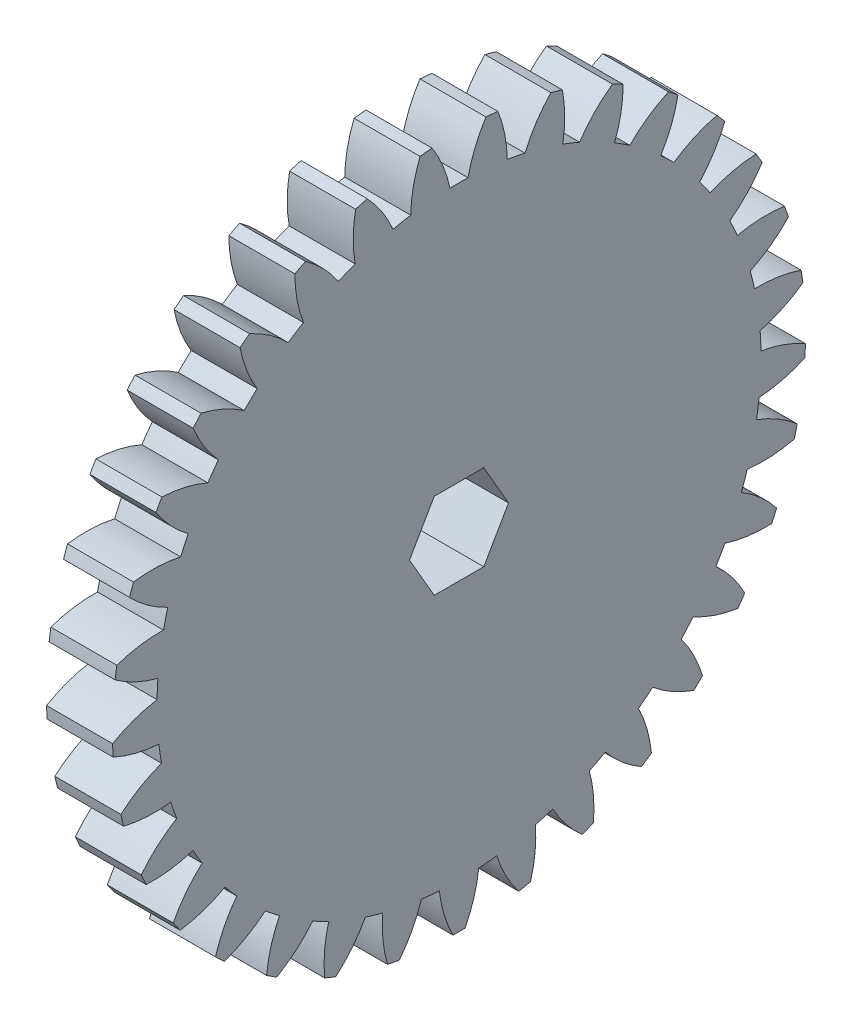
SolidWorks part; units mm, degrees
ref_plane "Plane1" through (0, 0, 0) normal (0, 0, 1) x (1, 0, 0)
ref_plane "Plane2" through (0, 0, 0) normal (0, 1, 0) x (1, 0, 0)
ref_plane "Plane3" through (0, 0, 0) normal (1, 0, 0) x (0, 0, -1)
sketch "HoldingSke" plane through (0, 0, 0) normal (0, 1, 0) x (1, 0, 0)
  line L0 (0, 0) -> (0.5591, -0.3631)
  line L1 (-15, 0) -> (100, 0) construction
  line L2 (0, 0) -> (-2.1039, 2.3779)
  line L3 (0, 0) -> (-11.863, 4.5341)
  line L4 (0, 0) -> (7.2428, 4.7035)
  line L5 (0, 0) -> (-46.8476, -17.4728)
  line L6 (0, 0) -> (-4.1448, -2.7965)
  line L7 (-2.1039, 2.3779) -> (8.6586, 51.2059)
  line L8 (-76.2, 54.61) -> (-75.3, 54.61)
  line L9 (-71.009, 38.7566) -> (-53.1078, 45.2721)
  line L10 (-76.2, 71.12) -> (104.1128, 71.12)
  line L11 (0, 0) -> (-5, 0)
  line L12 (-76.2, 101.6) -> (-76.147, 101.6)
  line L13 (24.9733, 27.94) -> (52.9518, 28.4284)
  line L14 (24.9733, 27.94) -> (24.9743, 27.94)
  line L15 (24.9733, 27.94) -> (100.4006, 29.5858)
  line L16 (-63.627, -1.5) -> (-12.827, -1.5)
  circle A0 centre (0, 0) radius 2.5
  circle A1 centre (0, 0) radius 22.874
  circle A2 centre (0, 0) radius 37.5
  circle A3 centre (0, 0) radius 2.5
  dimension "MHD" = 45.748
  dimension "Hub_dia" = 75
  dimension "Bore" = 5
  dimension "MBD" = 5
  dimension "Num_teeth" = 33
  dimension "Pitch" = 0.6667
  dimension "Overall_len" = 50
  dimension "Show_teeth" = 33
  dimension "Thickness" = 5
  dimension "OAL" = 50.0001
  dimension "T_dim" = 0.9
  dimension "Ap" = 20
  dimension "H" = 19.05
  dimension "Pitch_radius" = 180.3128
  dimension "Width" = 5
  dimension "Backlash" = 0.053
  dimension "Addendum_fac" = 1
  dimension "Dedendum_fac" = 1.25
  dimension "Clearance_fac" = 0.25
  dimension "Dedendum_add" = 0.001
  dimension "Module" = 1.5
sketch "BasProSke" plane through (0, 0, 0) normal (0, 1, 0) x (1, 0, 0)
  line L0 (-10, 0) -> (60, 0) construction
  line L1 (0, 0) -> (0, 26.25)
  line L2 (0, 0) -> (5, 0)
  line L3 (5, 0) -> (5, 26.25)
  line L4 (5, 26.25) -> (0, 26.25)
  dimension "Thickness" = 5
  dimension "Diameter" = 52.5
revolve "Base-Revolve" add sketch "BasProSke" angle 360 about L0
sketch "TooCutSke" plane through (0, 0, 0) normal (1, 0, 0) x (0, 0, -1)
  line L1 (0, 0) -> (0, 107) construction
  line L2 (0, 0) -> (-1.2704, 24.7174) construction
  line L3 (0, 0) -> (-4.7008, 49.2285) construction
  line L4 (-1.2704, 24.7174) -> (-2.3504, 24.6142) construction
  arc A0 (0.6837, 22.8638) -> (-0.6837, 22.8638) centre (0, 0) ccw
  arc A1 (2.0575, 26.1947) -> (-2.0575, 26.1947) centre (0, 0) ccw
  circle A2 centre (0, 0) radius 24.75 construction
  circle A3 centre (0, 0) radius 23.2574 construction
  arc A4 (-0.6837, 22.8638) -> (-2.0575, 26.1947) centre (-10.3699, 20.8176) ccw
  arc A5 (2.0575, 26.1947) -> (0.6837, 22.8638) centre (10.3699, 20.8176) ccw
  dimension "Root_dia" = 45.748
  dimension "Overcut_dia" = 52.5508
  dimension "Pitch_dia" = 49.5
  dimension "Base_dia" = 46.5148
  dimension "Flank_rad" = 9.9
  dimension "Half_ang" = 5.455
  dimension "Half_CT" = 1.0849
extrude "ToothCut" cut sketch "TooCutSke" along normal through all
fillet "Breaks" [suppressed] radius 0.03
fillet "RootFillets" [suppressed] radius 0.376
pattern_circular "TeethCuts" count 33 every 10.909 about axis through (-10, 0, 0) along (1, 0, 0) of "ToothCut", "RootFillets", "Breaks"
sketch "HubNeaOneSke" plane through (0, 0, 0) normal (-1, 0, 0) x (0, 0, 1)
  circle A0 centre (0, 0) radius 22.874
  dimension "Diameter" = 45.748
extrude "HubNearOne" [suppressed] add sketch "HubNeaOneSke" along normal blind 45.0001
sketch "HubNeaBotSke" plane through (0, 0, 0) normal (-1, 0, 0) x (0, 0, 1)
  circle A0 centre (0, 0) radius 22.874
  dimension "Diameter" = 45.748
extrude "HubNearBoth" [suppressed] add sketch "HubNeaBotSke" along normal blind 22.5
ref_plane "FarPln" through (5, 0, 0) normal (1, 0, 0) x (0, 0, -1)
sketch "HubFarSke" plane through (5, 0, 0) normal (1, 0, 0) x (0, 0, -1)
  circle A0 centre (0, 0) radius 22.874
  dimension "Diameter" = 45.748
extrude "HubFar" [suppressed] add sketch "HubFarSke" along normal blind 22.5
sketch "BorSke" plane through (0, 0, 0) normal (1, 0, 0) x (0, 0, -1)
  line L1 (-3.75, 0) -> (-1.875, -3.2476)
  line L2 (-1.875, -3.2476) -> (1.875, -3.2476)
  line L3 (1.875, -3.2476) -> (3.75, 0)
  line L4 (3.75, 0) -> (1.875, 3.2476)
  line L5 (1.875, 3.2476) -> (-1.875, 3.2476)
  line L6 (-1.875, 3.2476) -> (-3.75, 0)
  circle A0 centre (0, 0) radius 3.75 construction
  circle A1 centre (0, 0) radius 3.2476 construction
  dimension "Diameter" = 7.5
extrude "Bore" cut sketch "BorSke" along normal mid plane 100.0001
sketch "KeySke" plane through (0, 0, 0) normal (1, 0, 0) x (0, 0, -1)
  line L0 (-1, 0) -> (-1, 3.4)
  line L1 (-1, 3.4) -> (1, 3.4)
  line L2 (1, 3.4) -> (1, 0)
  line L3 (0, 0) -> (0, 34) construction
  line L4 (-1, 0) -> (1, 0)
  dimension "Offset" = 3.4
  dimension "Width" = 2
extrude "Keyway" [suppressed] cut sketch "KeySke" along normal mid plane 100.0001
pattern_circular "Keyway2" [suppressed] count 2 every 90 about axis through (-10, 0, 0) along (1, 0, 0)
sketch "Sketch1" plane through (0, 0, 0) normal (-1, 0, 0) x (0, 0, 1)
  line L0 (-1.875, -3.2476) -> (1.875, -3.2476) construction
  line L1 (-3.75, 0) -> (-1.875, -3.2476) construction
  line L2 (-1.875, 3.2476) -> (-3.75, 0) construction
  line L3 (1.875, 3.2476) -> (-1.875, 3.2476) construction
  line L4 (3.75, 0) -> (1.875, 3.2476) construction
  line L5 (1.875, -3.2476) -> (3.75, 0) construction
  line L6 (3.75, 0) -> (1.875, 3.2476)
  line L7 (1.875, 3.2476) -> (-1.875, 3.2476)
  line L8 (-1.875, 3.2476) -> (-3.75, 0)
  line L9 (-3.75, 0) -> (-1.875, -3.2476)
  line L10 (-1.875, -3.2476) -> (1.875, -3.2476)
  line L11 (1.875, -3.2476) -> (3.75, 0)
  arc A80 (0.1868, -8.9981) -> (0.8757, -5.5554) centre (-1.8542, -6.7994) ccw
  arc A81 (-0.1868, -8.9981) -> (0.1868, -8.9981) centre (0, 0) ccw
  arc A82 (-0.8757, -5.5554) -> (-0.1868, -8.9981) centre (1.8542, -6.7994) ccw
  arc A83 (-2.5569, -5.0091) -> (-0.8757, -5.5554) centre (0, 0) ccw
  arc A84 (-5.1378, -7.3894) -> (-2.5569, -5.0091) centre (-5.4967, -4.4109) ccw
  arc A85 (-5.4401, -7.1698) -> (-5.1378, -7.3894) centre (0, 0) ccw
  arc A86 (-3.9738, -3.9797) -> (-5.4401, -7.1698) centre (-2.4965, -6.5907) ccw
  arc A87 (-5.0129, -2.5496) -> (-3.9738, -3.9797) centre (0, 0) ccw
  arc A88 (-8.4999, -2.9582) -> (-5.0129, -2.5496) centre (-7.0396, -0.3377) ccw
  arc A89 (-8.6154, -2.6029) -> (-8.4999, -2.9582) centre (0, 0) ccw
  arc A90 (-5.5541, -0.8839) -> (-8.6154, -2.6029) centre (-5.8936, -3.8646) ccw
  arc A91 (-5.5541, 0.8839) -> (-5.5541, -0.8839) centre (0, 0) ccw
  arc A92 (-8.6154, 2.6029) -> (-5.5541, 0.8839) centre (-5.8936, 3.8646) ccw
  arc A93 (-8.4999, 2.9582) -> (-8.6154, 2.6029) centre (0, 0) ccw
  arc A94 (-5.0129, 2.5496) -> (-8.4999, 2.9582) centre (-7.0396, 0.3377) ccw
  arc A95 (-3.9738, 3.9797) -> (-5.0129, 2.5496) centre (0, 0) ccw
  arc A96 (-5.4401, 7.1698) -> (-3.9738, 3.9797) centre (-2.4965, 6.5907) ccw
  arc A97 (-5.1378, 7.3894) -> (-5.4401, 7.1698) centre (0, 0) ccw
  arc A98 (-2.5569, 5.0091) -> (-5.1378, 7.3894) centre (-5.4967, 4.4109) ccw
  arc A99 (-0.8757, 5.5554) -> (-2.5569, 5.0091) centre (0, 0) ccw
  arc A100 (-0.1868, 8.9981) -> (-0.8757, 5.5554) centre (1.8542, 6.7994) ccw
  arc A101 (0.1868, 8.9981) -> (-0.1868, 8.9981) centre (0, 0) ccw
  arc A102 (0.8757, 5.5554) -> (0.1868, 8.9981) centre (-1.8542, 6.7994) ccw
  arc A103 (2.5569, 5.0091) -> (0.8757, 5.5554) centre (0, 0) ccw
  arc A104 (5.1378, 7.3894) -> (2.5569, 5.0091) centre (5.4967, 4.4109) ccw
  arc A105 (5.4401, 7.1698) -> (5.1378, 7.3894) centre (0, 0) ccw
  arc A106 (3.9738, 3.9797) -> (5.4401, 7.1698) centre (2.4965, 6.5907) ccw
  arc A107 (5.0129, 2.5496) -> (3.9738, 3.9797) centre (0, 0) ccw
  arc A108 (8.4999, 2.9582) -> (5.0129, 2.5496) centre (7.0396, 0.3377) ccw
  arc A109 (8.6154, 2.6029) -> (8.4999, 2.9582) centre (0, 0) ccw
  arc A110 (5.5541, 0.8839) -> (8.6154, 2.6029) centre (5.8936, 3.8646) ccw
  arc A111 (5.5541, -0.8839) -> (5.5541, 0.8839) centre (0, 0) ccw
  arc A112 (8.6154, -2.6029) -> (5.5541, -0.8839) centre (5.8936, -3.8646) ccw
  arc A113 (8.4999, -2.9582) -> (8.6154, -2.6029) centre (0, 0) ccw
  arc A114 (5.0129, -2.5496) -> (8.4999, -2.9582) centre (7.0396, -0.3377) ccw
  arc A115 (3.9738, -3.9797) -> (5.0129, -2.5496) centre (0, 0) ccw
  arc A116 (5.4401, -7.1698) -> (3.9738, -3.9797) centre (2.4965, -6.5907) ccw
  arc A117 (5.1378, -7.3894) -> (5.4401, -7.1698) centre (0, 0) ccw
  arc A118 (2.5569, -5.0091) -> (5.1378, -7.3894) centre (5.4967, -4.4109) ccw
  arc A119 (0.8757, -5.5554) -> (2.5569, -5.0091) centre (0, 0) ccw
extrude "Boss-Extrude1" add sketch "Sketch1" along normal blind 6
equation "' \"Module@HoldingSke\" = 6.35"
equation "' \"Num_teeth@HoldingSke\" = 12"
equation "' \"Ap@HoldingSke\" =  20"
equation "' \"Ap@HoldingSke\" = 20"
equation "' \"Width@HoldingSke\" = 0.5 * 25.4"
equation "' \"Hub_dia@HoldingSke\"= 1 * 25.4"
equation "' \"Hub_dia@HoldingSke\" = 1 * 25.4"
equation "' \"Overall_len@HoldingSke\" = 1.0 * 25.4"
equation "' \"Bore@HoldingSke\" = 0.75 * 25.4"
equation "' \"T_dim@HoldingSke\" = 0.1 * 25.4"
equation "' \"Width@KeySke\" = 0.25 * 25.4"
equation "' \"Show_teeth@HoldingSke\" = 13"
equation "' \"Backlash@HoldingSke\" = 0.009 * 25.4"
equation "' \"Addendum_fac@HoldingSke\" = 1.0"
equation "' \"Dedendum_fac@HoldingSke\" = 1.25"
equation "' \"Dedendum_add@HoldingSke\" = 0.00005 * 25.4"
equation "' \"Clearance_fac@HoldingSke\" = 0.25"
equation "\"Pitch@HoldingSke\" = 1 / \"Module@HoldingSke\""
equation "\"Overcut_dia@TooCutSke\" = (\"Num_teeth@HoldingSke\" + 2 * \"Addendum_fac@HoldingSke\") / \"Pitch@HoldingSke\" + 0.002 * 25.4"
equation "\"Pitch_dia@TooCutSke\" = \"Num_teeth@HoldingSke\" / \"Pitch@HoldingSke\""
equation "\"Base_dia@TooCutSke\" = \"Num_teeth@HoldingSke\" / \"Pitch@HoldingSke\" * cos((\"Ap@HoldingSke\"  * 3.14159265 / 180))"
equation "\"Root_dia@TooCutSke\" = (\"Num_teeth@HoldingSke\" + 2) / \"Pitch@HoldingSke\" - 2 * (\"Addendum_fac@HoldingSke\" + \"Dedendum_fac@HoldingSke\") / \"Pitch@HoldingSke\" - \"Dedendum_add@HoldingSke\" * 2"
equation "\"Half_ang@TooCutSke\" = 180 / \"Num_teeth@HoldingSke\""
equation "\"Half_CT@TooCutSke\" = \"Num_teeth@HoldingSke\" / \"Pitch@HoldingSke\" * sin((3.14159265 / 2 / \"Num_teeth@HoldingSke\")) / 2 - 7 * \"Backlash@HoldingSke\" / 4"
equation "\"Flank_rad@TooCutSke\" = \"Num_teeth@HoldingSke\" / \"Pitch@HoldingSke\" / 5"
equation "\"Radius@RootFillets\" = \"Clearance_fac@HoldingSke\" / \"Pitch@HoldingSke\" + \"Dedendum_add@HoldingSke\""
equation "\"Break_rad@Breaks\" = 0.02 / \"Pitch@HoldingSke\""
equation "\"Thickness@HoldingSke\" = \"Width@HoldingSke\""
equation "\"OAL@HoldingSke\" = \"Thickness@HoldingSke\""
equation "\"MHD@HoldingSke\" = (\"Num_teeth@HoldingSke\" + 2) / \"Pitch@HoldingSke\" - 2 * (\"Addendum_fac@HoldingSke\" + \"Dedendum_fac@HoldingSke\")  / \"Pitch@HoldingSke\" - \"Dedendum_add@HoldingSke\" * 2"
equation "\"MBD@HoldingSke\" = (\"Num_teeth@HoldingSke\" + 2) / \"Pitch@HoldingSke\" - 2 * (\"Addendum_fac@HoldingSke\" + \"Dedendum_fac@HoldingSke\")  / \"Pitch@HoldingSke\" - \"Dedendum_add@HoldingSke\" * 2 - 0.002 * 25.4"
equation "\"MHD@HoldingSke\" = ((sgn( \"MHD@HoldingSke\" - \"Hub_dia@HoldingSke\" )-1)*( \"MHD@HoldingSke\" - \"Hub_dia@HoldingSke\" ))/-2+ \"Hub_dia@HoldingSke\""
equation "\"MBD@HoldingSke\" = ((sgn( \"MBD@HoldingSke\" - \"Bore@HoldingSke\" )-1)*( \"MBD@HoldingSke\" - \"Bore@HoldingSke\" ))/-2+ \"Bore@HoldingSke\""
equation "\"OAL@HoldingSke\" = ((sgn( \"OAL@HoldingSke\" - \"Overall_len@HoldingSke\" )+1)*( \"OAL@HoldingSke\" - \"Overall_len@HoldingSke\" ))/2 + \"Overall_len@HoldingSke\" + 0.000002 * 25.4"
equation "\"Num_teeth@TeethCuts\" = int( \"Show_teeth@HoldingSke\" ) + 1"
equation "\"Num_teeth@TeethCuts\" = ((sgn( \"Num_teeth@TeethCuts\" - \"Num_teeth@HoldingSke\" )-1)*( \"Num_teeth@TeethCuts\" - \"Num_teeth@HoldingSke\" ))/-2+ \"Num_teeth@HoldingSke\""
equation "\"Num_teeth@TeethCuts\" = ((sgn( \"Num_teeth@TeethCuts\" - 2.0)+1)*( \"Num_teeth@TeethCuts\" - 2.0))/2 +2.0"
equation "\"Angle@TeethCuts\" = 360.0 / \"Num_teeth@HoldingSke\""
equation "\"Diameter@BasProSke\" = (\"Num_teeth@HoldingSke\" + 2 * \"Addendum_fac@HoldingSke\") / \"Pitch@HoldingSke\""
equation "\"Thickness@BasProSke\"  = \"Thickness@HoldingSke\""
equation "' \"Fillet_rad@BasProSke\" =  \"Thickness@HoldingSke\" * 0.05"
equation "' \"Fillet_rad@BasProSke\" = \"Thickness@HoldingSke\" * 0.05"
equation "\"MHD@HoldingSke\" = ((sgn( \"MHD@HoldingSke\" - \"Root_dia@TooCutSke\" )-1)*( \"MHD@HoldingSke\" - \"Root_dia@TooCutSke\" ))/-2+ \"Root_dia@TooCutSke\""
equation "\"Diameter@HubNeaOneSke\" = \"MHD@HoldingSke\""
equation "\"Length@HubNearOne\" = \"OAL@HoldingSke\" - \"Thickness@BasProSke\""
equation "\"Diameter@HubNeaBotSke\" = \"MHD@HoldingSke\""
equation "\"Length@HubNearBoth\" = ( \"OAL@HoldingSke\" - \"Thickness@BasProSke\" ) / 2.0"
equation "\"Thickness@FarPln\" = \"Thickness@BasProSke\""
equation "\"Diameter@HubFarSke\" = \"MHD@HoldingSke\""
equation "\"Length@HubFar\" = ( \"OAL@HoldingSke\" - \"Thickness@BasProSke\" ) / 2.0"
equation "\"Diameter@BorSke\"=7.5"
equation "\"D1@Bore\" = \"OAL@HoldingSke\" * 2.0"
equation "\"D1@Keyway\" = \"OAL@HoldingSke\" * 2.0"
equation "\"Offset@KeySke\" = \"T_dim@HoldingSke\" + \"MBD@HoldingSke\" / 2.0"
